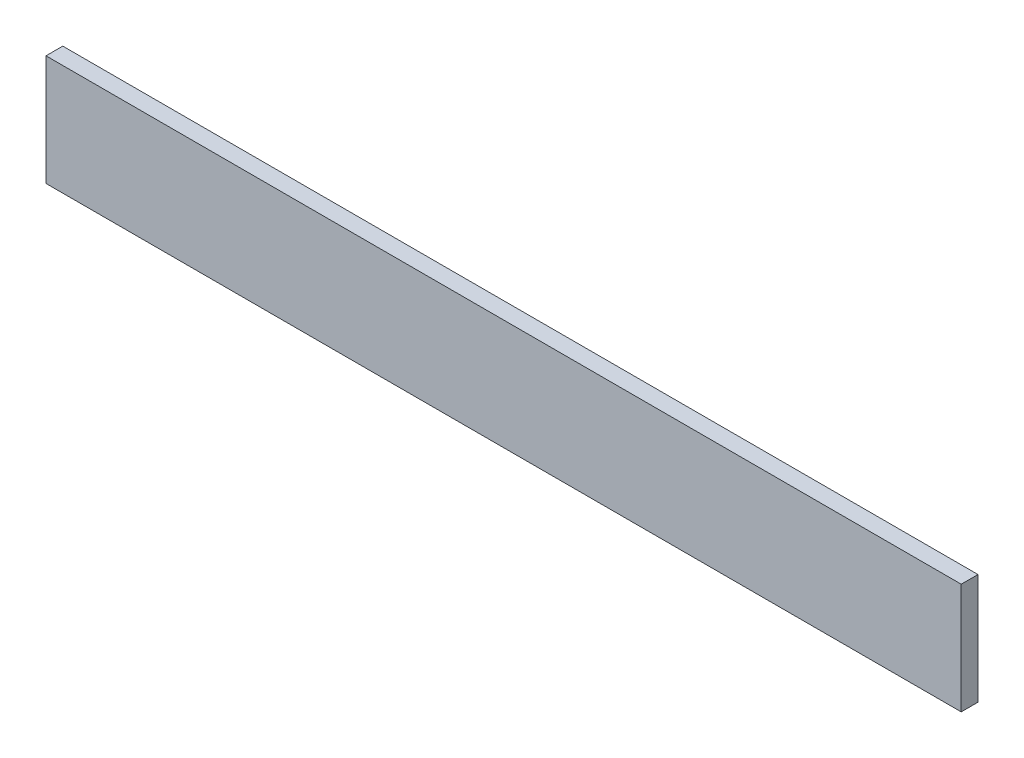
SolidWorks part; units mm, degrees
material "Pine"
ref_plane "Front Plane" through (0, 0, 0) normal (0, 0, 1) x (1, 0, 0)
ref_plane "Top Plane" through (0, 0, 0) normal (0, 1, 0) x (1, 0, 0)
ref_plane "Right Plane" through (0, 0, 0) normal (1, 0, 0) x (0, 0, -1)
sketch "Sketch1" plane through (0, 0, 0) normal (0, 0, 1) x (1, 0, 0)
  line L1 (600, 72.5) -> (-600, 72.5)
  line L2 (600, 72.5) -> (600, -72.5)
  line L3 (600, -72.5) -> (-600, -72.5)
  line L4 (-600, 72.5) -> (-600, -72.5)
  point P4 (-600, 0)
  point P5 (0, -72.5)
  dimension "D1" = 145
  dimension "D2" = 1200
extrude "Boss-Extrude1" add sketch "Sketch1" along normal blind 22
